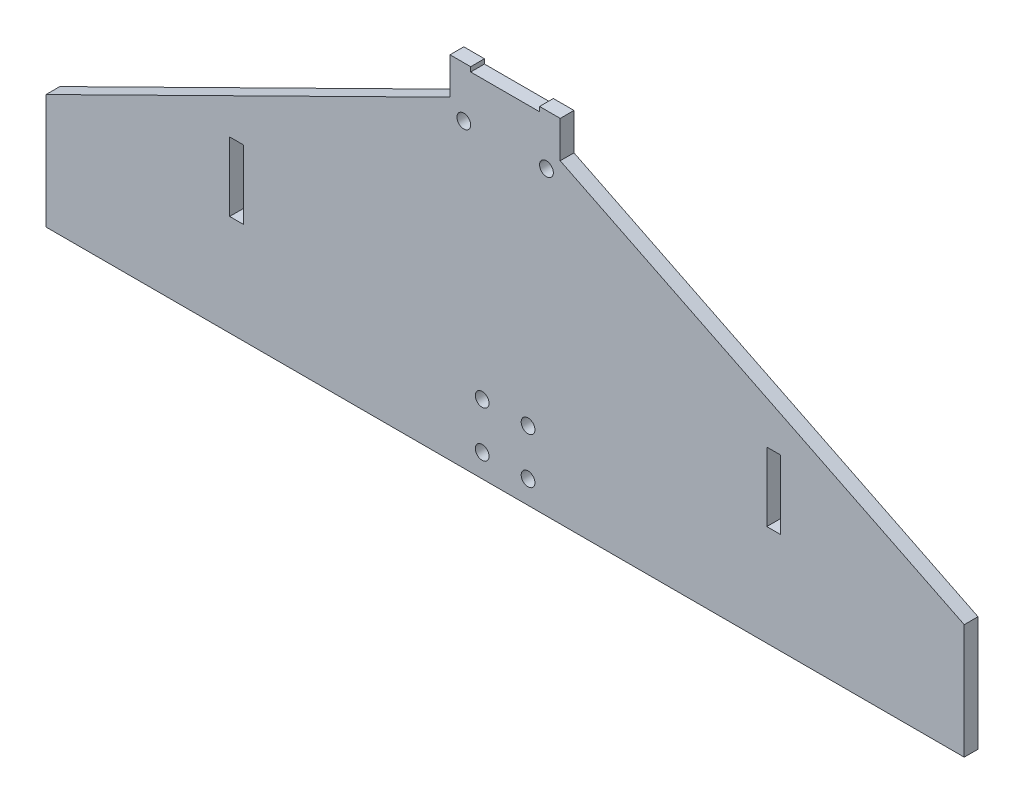
SolidWorks part; units mm, degrees
ref_plane "前视基准面" through (0, 0, 0) normal (0, 0, 1) x (1, 0, 0)
ref_plane "上视基准面" through (0, 0, 0) normal (0, 1, 0) x (1, 0, 0)
ref_plane "右视基准面" through (0, 0, 0) normal (1, 0, 0) x (0, 0, -1)
sketch "草图2" plane through (0, 0, 0) normal (0, 0, 1) x (1, 0, 0)
  line L1 (-7.5, 56.5) -> (-7.5, 55.5)
  line L6 (-100, -20) -> (100, -20)
  line L8 (7.5, 55.5) -> (-7.5, 55.5)
  line L9 (-12, 48.5) -> (-100, 5)
  line L10 (-100, 5) -> (-100, -20)
  line L11 (12, 48.5) -> (100, 5)
  line L16 (100, 5) -> (100, -20)
  line L17 (-12, 48.5) -> (-12, 56.5)
  line L20 (7.5, 56.5) -> (7.5, 55.5)
  line L24 (-7.5, 56.5) -> (-12, 56.5)
  line L26 (7.5, 56.5) -> (12, 56.5)
  line L27 (0, 55.5) -> (0, -20) construction
  line L28 (12, 48.5) -> (12, 56.5)
  dimension "D1" = 25
  dimension "D2" = 200
  dimension "D3" = 7
  dimension "D4" = 24
  dimension "D5" = 1
  dimension "D6" = 75.5
extrude "凸台-拉伸1" add sketch "草图2" along normal blind 3
sketch "草图4" plane through (0, 0, 3) normal (0, 0, 1) x (1, 0, 0)
  line L0 (-100, -20) -> (100, -20) construction
  line L1 (-5, -5) -> (5, -5) construction
  line L2 (-5, -5) -> (-5, -15) construction
  line L3 (-5, -15) -> (5, -15) construction
  line L4 (5, -5) -> (5, -15) construction
  circle A0 centre (-5, -5) radius 1.5
  circle A1 centre (5, -5) radius 1.5
  circle A2 centre (-5, -15) radius 1.5
  circle A3 centre (5, -15) radius 1.5
  point P8 (0, -5)
  dimension "D3" = 3
  dimension "D1" = 10
  dimension "D2" = 10
  dimension "D4" = 5
extrude "切除-拉伸2" cut sketch "草图4" against normal blind 5
sketch "草图6" plane through (0, 0, 3) normal (0, 0, 1) x (1, 0, 0)
  line L0 (-9, 45.5) -> (9, 45.5) construction
  line L1 (7.5, 55.5) -> (-7.5, 55.5) construction
  circle A0 centre (-9, 45.5) radius 1.5
  circle A1 centre (9, 45.5) radius 1.5
  point P4 (0, 45.5)
  dimension "D2" = 3
  dimension "D1" = 18
  dimension "D3" = 10
extrude "切除-拉伸4" cut sketch "草图6" against normal blind 5
sketch "草图7" plane through (0, 0, 3) normal (0, 0, 1) x (1, 0, 0)
  line L0 (0, 55.5) -> (0, -20) construction
  line L1 (-60, 17) -> (-57, 17)
  line L2 (-60, 17) -> (-60, 2)
  line L3 (-60, 2) -> (-57, 2)
  line L4 (-57, 17) -> (-57, 2)
  line L5 (7.5, 55.5) -> (-7.5, 55.5) construction
  line L6 (-100, -20) -> (100, -20) construction
  line L7 (57, 17) -> (57, 2)
  line L8 (60, 2) -> (57, 2)
  line L9 (60, 17) -> (60, 2)
  line L10 (60, 17) -> (57, 17)
  dimension "D1" = 120
  dimension "D2" = 3
  dimension "D3" = 15
  dimension "D4" = 22
extrude "切除-拉伸5" cut sketch "草图7" against normal blind 10
